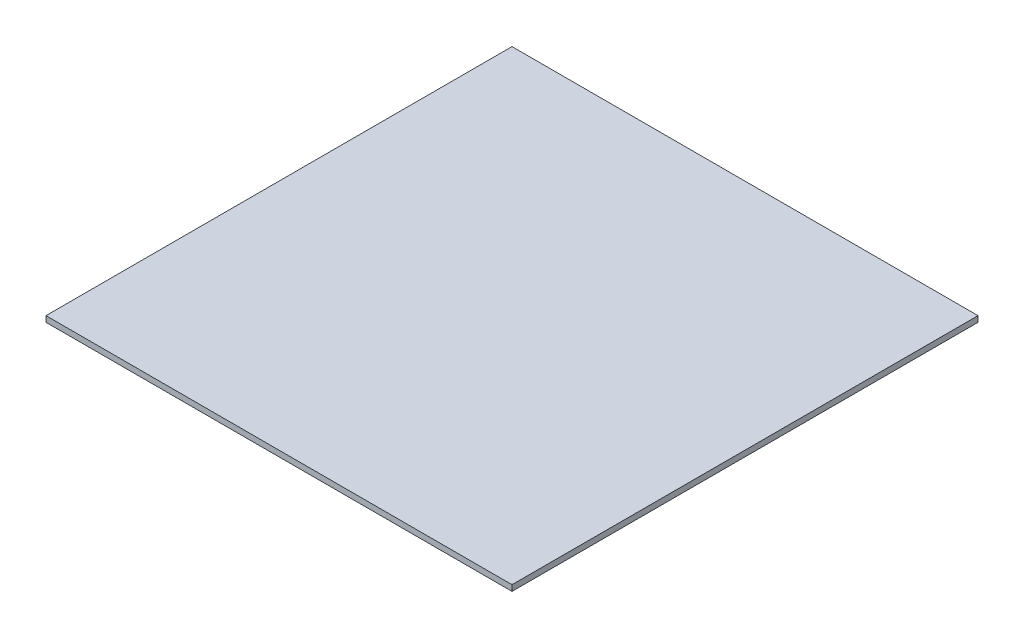
SolidWorks part; units mm, degrees
ref_plane "Front Plane" through (0, 0, 0) normal (0, 0, 1) x (1, 0, 0)
ref_plane "Top Plane" through (0, 0, 0) normal (0, 1, 0) x (1, 0, 0)
ref_plane "Right Plane" through (0, 0, 0) normal (1, 0, 0) x (0, 0, -1)
sketch "Sketch1" plane through (0, 0, 0) normal (0, 1, 0) x (1, 0, 0)
  line L1 (0, 0) -> (-160, 0)
  line L2 (0, 0) -> (0, 160)
  line L3 (0, 160) -> (-160, 160)
  line L4 (-160, 0) -> (-160, 160)
  dimension "D1" = 160
  dimension "D2" = 160
extrude "Boss-Extrude1" add sketch "Sketch1" along normal blind 2
